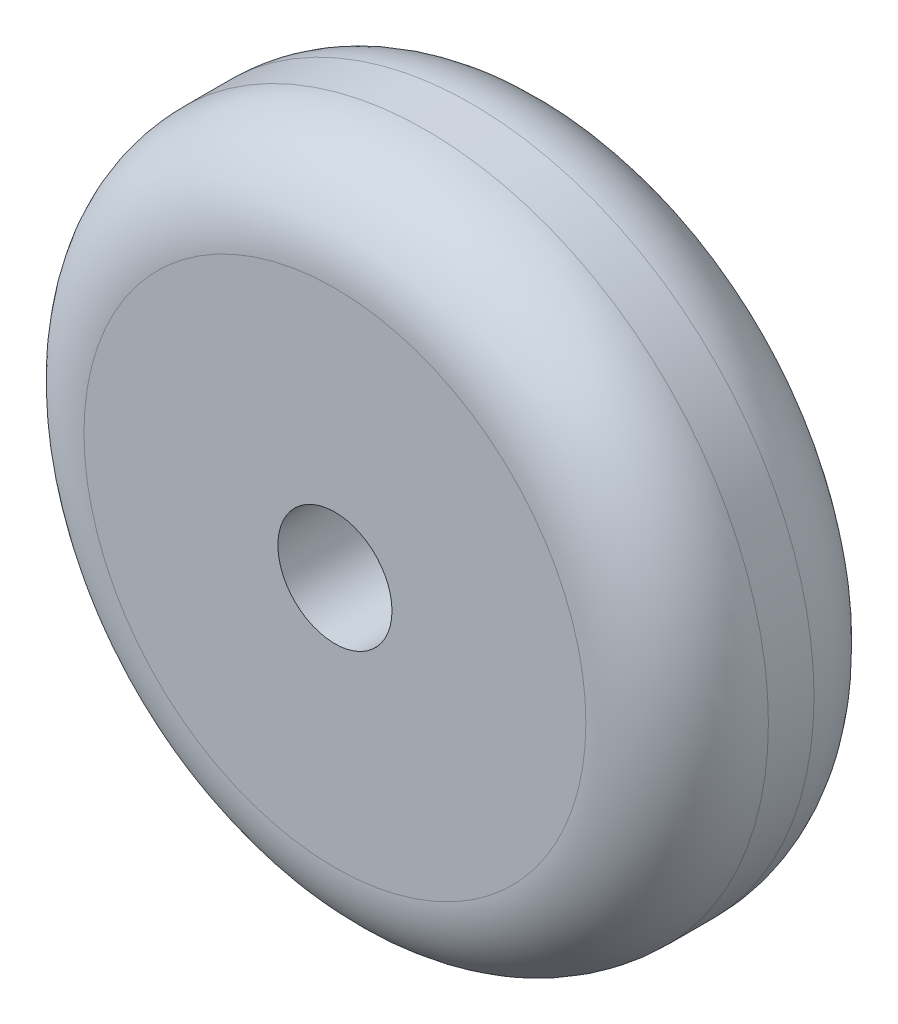
SolidWorks part; units mm, degrees
material "Rubber"
ref_plane "Front Plane" through (0, 0, 0) normal (0, 0, 1) x (1, 0, 0)
ref_plane "Top Plane" through (0, 0, 0) normal (0, 1, 0) x (1, 0, 0)
ref_plane "Right Plane" through (0, 0, 0) normal (1, 0, 0) x (0, 0, -1)
sketch "Sketch1" plane through (0, 0, 0) normal (0, 0, 1) x (1, 0, 0)
  circle A0 centre (0, 0) radius 75
  dimension "D1" = 150
extrude "Boss-Extrude1" add sketch "Sketch1" along normal blind 50
fillet "Fillet2" radius 20 1 edges at (75, 0, 50)
fillet "Fillet3" radius 20 1 edges at (75, 0, 0)
sketch "Sketch2" plane through (0, 0, 50) normal (0, 0, 1) x (1, 0, 0)
  circle A0 centre (0, 0) radius 12.5
  dimension "D1" = 25
extrude "Cut-Extrude1" cut sketch "Sketch2" against normal through all
